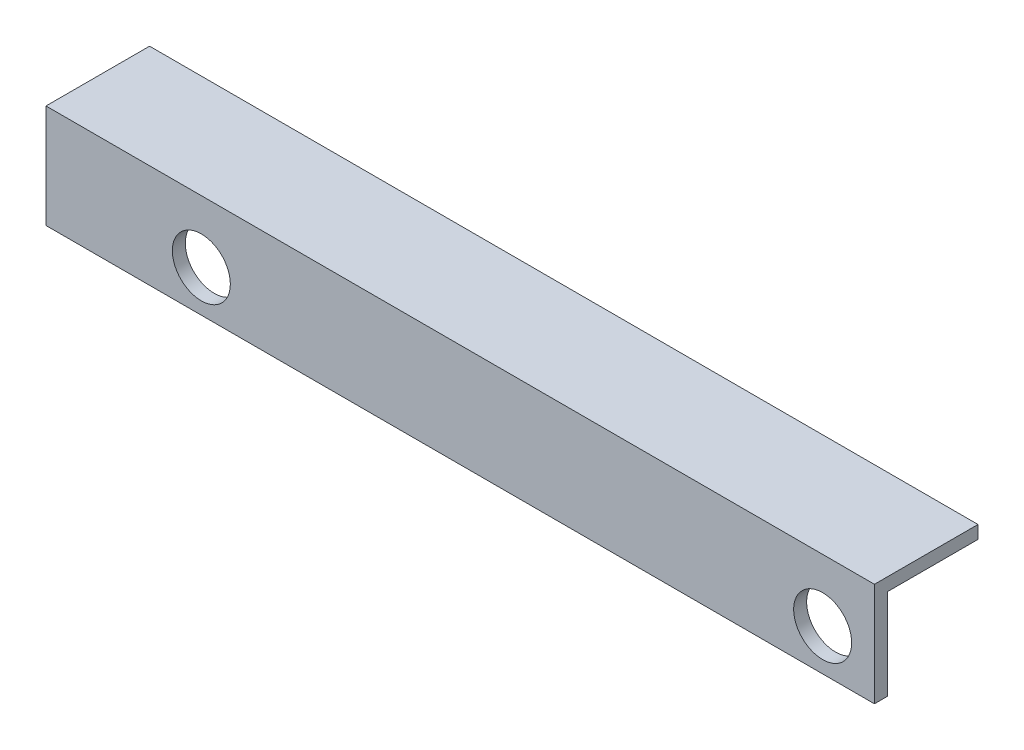
SolidWorks part; units mm, degrees
material "5052-H32"
ref_plane "Front Plane" through (0, 0, 0) normal (0, 0, 1) x (1, 0, 0)
ref_plane "Top Plane" through (0, 0, 0) normal (0, 1, 0) x (1, 0, 0)
ref_plane "Right Plane" through (0, 0, 0) normal (1, 0, 0) x (0, 0, -1)
sketch "Sketch1" plane through (0, 0, 0) normal (1, 0, 0) x (0, 0, -1)
  line L0 (0, 0) -> (0, 12.7)
  line L1 (0, 55) -> (0, -55) construction
  line L2 (0, 12.7) -> (12.7, 12.7)
  line L3 (1.5875, 0) -> (1.5875, 11.1125)
  line L4 (1.5875, 11.1125) -> (12.7, 11.1125)
  line L5 (12.7, 12.7) -> (12.7, 11.1125)
  line L6 (0, 0) -> (1.5875, 0)
  dimension "D1" = 12.7
  dimension "D2" = 12.7
  dimension "D3" = 1.5875
extrude "Boss-Extrude1" add sketch "Sketch1" along normal blind 44.45 and the other way blind 57.15
sketch "Sketch3" plane through (0, 0, 0) normal (0, 0, 1) x (1, 0, 0)
  line L0 (-57.15, 12.7) -> (44.45, 12.7) construction
  line L1 (44.45, 12.7) -> (44.45, 0) construction
  line L2 (-38.1, 5.08) -> (38.1, 5.08) construction
  circle A0 centre (-38.1, 5.08) radius 3.556
  circle A1 centre (38.1, 5.08) radius 3.556
  dimension "D1" = 7.112
  dimension "D2" = 7.62
  dimension "D3" = 76.2
  dimension "D4" = 6.35
extrude "Cut-Extrude1" cut sketch "Sketch3" against normal through all
